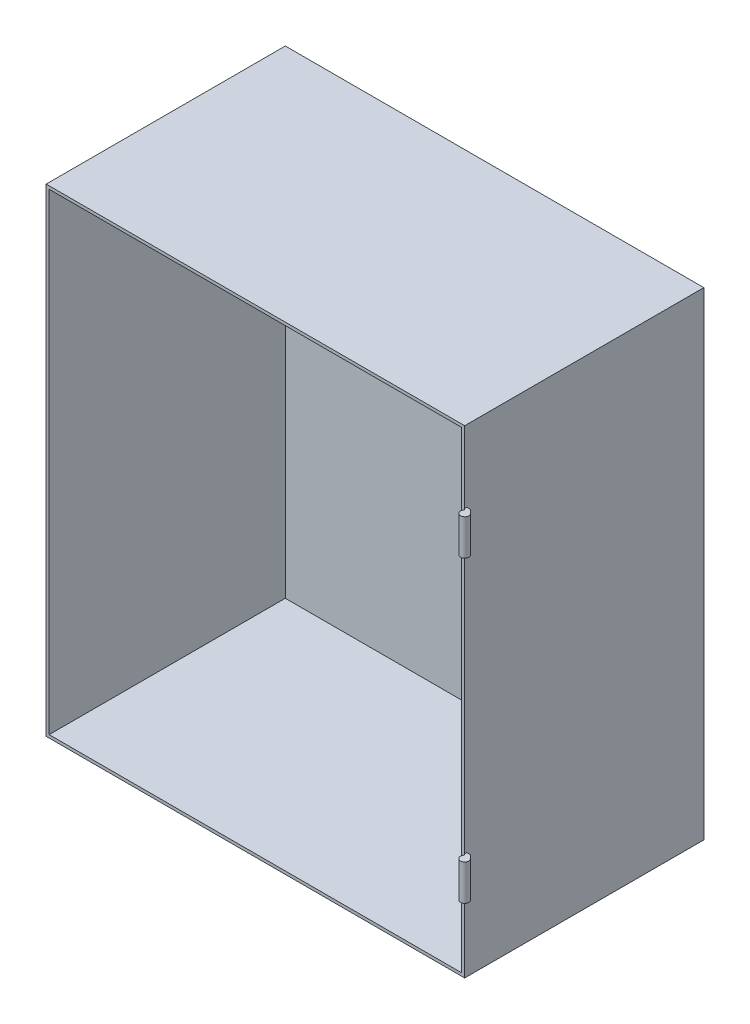
SolidWorks part; units mm, degrees
ref_plane "Alzado" through (0, 0, 0) normal (0, 0, 1) x (1, 0, 0)
ref_plane "Planta" through (0, 0, 0) normal (0, 1, 0) x (1, 0, 0)
ref_plane "Vista lateral" through (0, 0, 0) normal (1, 0, 0) x (0, 0, -1)
sketch "Croquis1" plane through (0, 0, 0) normal (0, 0, 1) x (1, 0, 0)
  line L1 (0, 0) -> (700, 0)
  line L2 (0, 0) -> (0, -800)
  line L3 (0, -800) -> (700, -800)
  line L4 (700, 0) -> (700, -800)
  dimension "D1" = 800
  dimension "D2" = 700
extrude "Saliente-Extruir1" add sketch "Croquis1" along normal blind 400
sketch "Croquis2" plane through (0, 0, 400) normal (0, 0, 1) x (1, 0, 0)
  line L8 (5, -5) -> (5, -795)
  line L9 (5, -795) -> (695, -795)
  line L10 (695, -795) -> (695, -5)
  line L11 (695, -5) -> (5, -5)
  line L12 (5, -5) -> (5, -795)
  line L13 (5, -795) -> (695, -795)
  line L14 (695, -795) -> (695, -5)
  line L15 (695, -5) -> (5, -5)
  dimension "D1" = 5
extrude "Cortar-Extruir1" cut sketch "Croquis2" against normal blind 395
sketch "Croquis3" plane through (0, 0, 0) normal (0, 1, 0) x (1, 0, 0)
  line L0 (700, -400) -> (707, -400) construction
  line L1 (707, -400) -> (707, -407) construction
  line L2 (700, -396.5459) -> (706, -396.5459)
  line L3 (700, -400) -> (700, 0) construction
  line L4 (706, -396.5459) -> (710.259, -400.8049)
  line L5 (700, -400) -> (702.0503, -402.0503)
  line L6 (700, -396.5459) -> (700, -400)
  arc A0 (702.0503, -402.0503) -> (710.259, -400.8049) centre (707, -407) ccw
  dimension "D3" = 6
  dimension "D1" = 7
  dimension "D2" = 7
extrude "Saliente-Extruir2" add sketch "Croquis3" against normal up to surface (800 mm away) up to face at (350, -800, 200)
sketch "Croquis4" plane through (0, 0, 0) normal (0, 0, -1) x (-1, 0, 0)
  line L0 (-700, -400) -> (-756.687, -400) construction
  line L1 (-700, 0) -> (-756.687, 0)
  line L2 (-700, 0) -> (-700, -120)
  line L3 (-700, -120) -> (-756.687, -120)
  line L4 (-756.687, 0) -> (-756.687, -120)
  line L5 (-700, -800) -> (-756.687, -800)
  line L6 (-700, -800) -> (-700, -680)
  line L7 (-700, -680) -> (-756.687, -680)
  line L8 (-756.687, -800) -> (-756.687, -680)
  line L9 (-700, -800) -> (-700, 0) construction
  line L10 (-700, -800) -> (-700, 0) construction
  line L11 (-756.687, -620) -> (-700, -620)
  line L12 (-756.687, -620) -> (-756.687, -180)
  line L13 (-756.687, -180) -> (-700, -180)
  line L14 (-700, -620) -> (-700, -180)
  line L15 (-756.687, -620) -> (-700, -180) construction
  line L16 (-756.687, -180) -> (-700, -620) construction
  point P14 (-728.3435, -400)
  dimension "D1" = 120
  dimension "D2" = 120
  dimension "D3" = 440
extrude "Cortar-Extruir2" cut sketch "Croquis4" against normal blind 450
